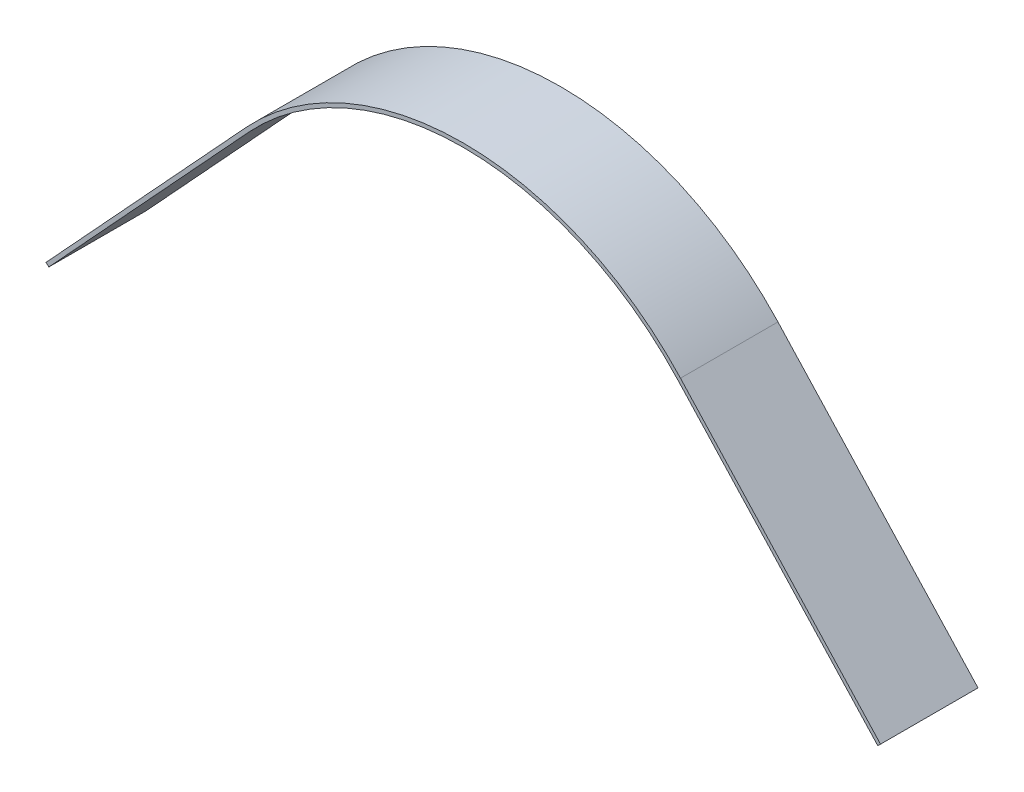
SolidWorks part; units mm, degrees
material "ABS"
ref_plane "Front Plane" through (0, 0, 0) normal (0, 0, 1) x (1, 0, 0)
ref_plane "Top Plane" through (0, 0, 0) normal (0, 1, 0) x (1, 0, 0)
ref_plane "Right Plane" through (0, 0, 0) normal (1, 0, 0) x (0, 0, -1)
sketch "Sketch1" plane through (0, 0, 0) normal (0, 0, 1) x (1, 0, 0)
  line L0 (-55.8669, 51.5256) -> (-108, -5)
  line L1 (55.8669, 51.5256) -> (108, -5)
  line L2 (-108, -5) -> (108, -5) construction
  arc A0 (55.8669, 51.5256) -> (-55.8669, 51.5256) centre (0, 0) ccw
  dimension "D1" = 76
  dimension "D2" = 216
  dimension "D3" = 5
extrude "Extrude-Thin1" add sketch "Sketch1" along normal mid plane 25.4 thin
